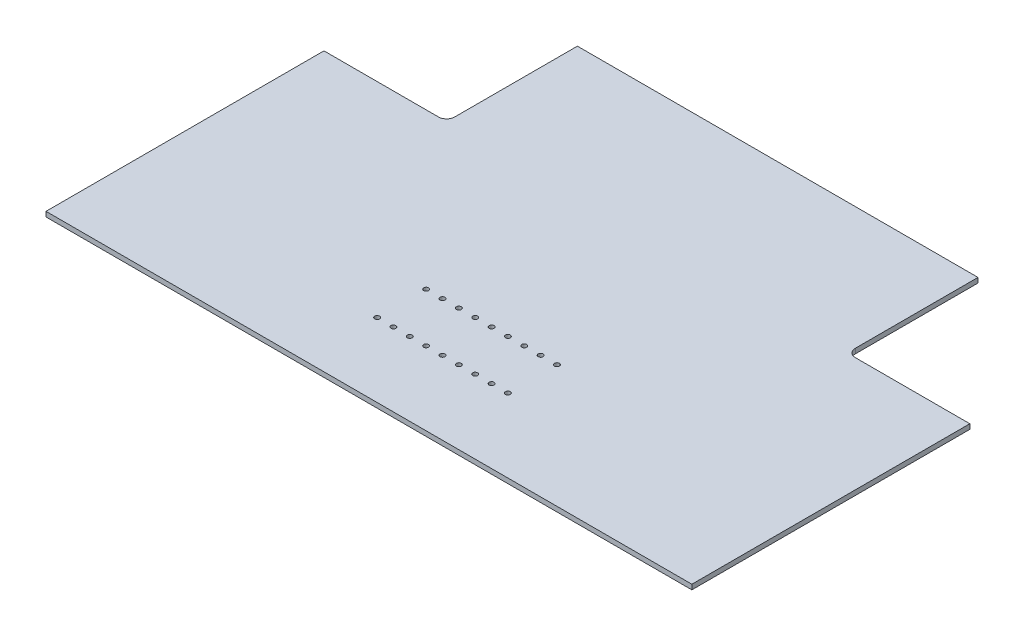
SolidWorks part; units mm, degrees
ref_plane "Front Plane" through (0, 0, 0) normal (0, 0, 1) x (1, 0, 0)
ref_plane "Top Plane" through (0, 0, 0) normal (0, 1, 0) x (1, 0, 0)
ref_plane "Right Plane" through (0, 0, 0) normal (1, 0, 0) x (0, 0, -1)
sketch "Sketch1" plane through (0, 0, 0) normal (0, 1, 0) x (1, 0, 0)
  line L1 (-197.5, 125) -> (197.5, 125)
  line L2 (-197.5, 125) -> (-197.5, -125)
  line L3 (-197.5, -125) -> (197.5, -125)
  line L4 (197.5, 125) -> (197.5, -125)
  line L5 (-197.5, 125) -> (197.5, -125) construction
  line L6 (-197.5, -125) -> (197.5, 125) construction
  point P0 (0, 0)
extrude "Boss-Extrude1" add sketch "Sketch1" along normal blind 3
sketch "Sketch2" plane through (0, 3, 0) normal (0, 1, 0) x (1, 0, 0)
  line L1 (-197.5, 125) -> (-122.5, 125)
  line L2 (-197.5, 125) -> (-197.5, 45)
  line L3 (-197.5, 45) -> (-122.5, 45)
  line L4 (-122.5, 125) -> (-122.5, 45)
extrude "Cut-Extrude1" cut sketch "Sketch2" against normal blind 3
mirror "Mirror1" about plane through (0, 0, 0) normal (1, 0, 0) of "Cut-Extrude1"
sketch "Sketch3" plane through (0, 3, 0) normal (0, 1, 0) x (1, 0, 0)
  circle A0 centre (0, -50) radius 1.5
  circle A1 centre (0, -80) radius 1.5
  point P4 (0, 0)
  point P5 (0, -2.0913)
  point P6 (0, 0)
  point P7 (0, 0)
  point P9 (0, 0)
  point P10 (0, 0)
  point P11 (0, 0)
  point P12 (0, 0)
  dimension "D1" = 30
  dimension "D2" = 50
extrude "Cut-Extrude2" cut sketch "Sketch3" against normal blind 10
fillet "Fillet1" radius 5 2 edges at (-122.5, 1.5, -45) (122.5, 1.5, -45)
pattern_linear "LPattern1" count 5 spacing 10 along (-1, 0, 0) count 5 spacing 10 along (1, 0, 0) of "Cut-Extrude2"
